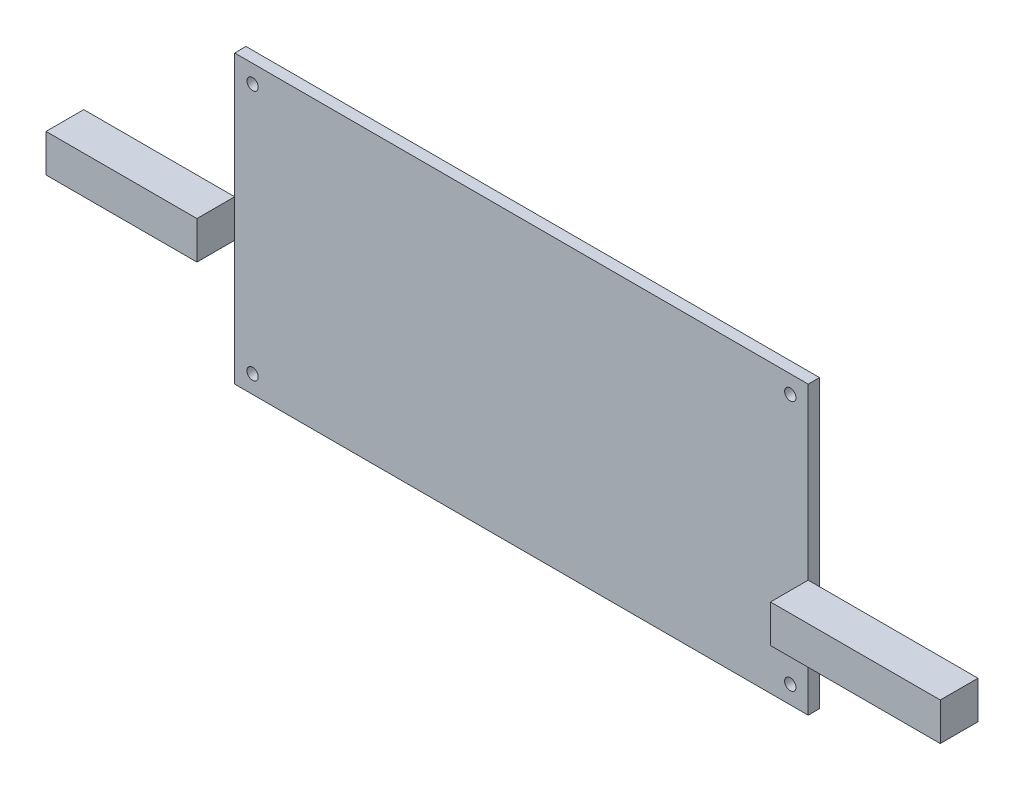
SolidWorks part; units mm, degrees
ref_plane "Front" through (0, 0, 0) normal (0, 0, 1) x (1, 0, 0)
ref_plane "Top" through (0, 0, 0) normal (0, 1, 0) x (1, 0, 0)
ref_plane "Right" through (0, 0, 0) normal (1, 0, 0) x (0, 0, -1)
sketch "Sketch1" plane through (0, 0, 0) normal (0, 0, 1) x (1, 0, 0)
  line L1 (-76, -38) -> (76, -38)
  line L2 (-76, -38) -> (-76, 38)
  line L3 (-76, 38) -> (76, 38)
  line L4 (76, -38) -> (76, 38)
  line L5 (-76, -38) -> (76, 38) construction
  line L6 (-76, 38) -> (76, -38) construction
  point P0 (0, 0)
  dimension "D1" = 152
  dimension "D2" = 76
extrude "Boss-Extrude1" add sketch "Sketch1" along normal mid plane 3
sketch "Sketch3" plane through (0, 0, 0) normal (0, 0, 1) x (1, 0, 0)
  line L1 (-71.25, -33.25) -> (71.25, -33.25) construction
  line L2 (-71.25, -33.25) -> (-71.25, 33.25) construction
  line L3 (-71.25, 33.25) -> (71.25, 33.25) construction
  line L4 (71.25, -33.25) -> (71.25, 33.25) construction
  line L5 (-71.25, -33.25) -> (71.25, 33.25) construction
  line L6 (-71.25, 33.25) -> (71.25, -33.25) construction
  circle A2 centre (-71.25, 33.25) radius 1.5
  circle A3 centre (71.25, 33.25) radius 1.5
  circle A4 centre (-71.25, -33.25) radius 1.5
  circle A5 centre (71.25, -33.25) radius 1.5
  point P0 (0, 0)
  point P10 (-71.25, -33.25)
  point P12 (71.25, -33.25)
  dimension "D3" = 3
  dimension "D1" = 142.5
  dimension "D2" = 66.5
extrude "Cut-Extrude1" cut sketch "Sketch3" against normal through all both and the other way through all
sketch "Sketch4" plane through (0, 0, 1.5) normal (0, 0, 1) x (1, 0, 0)
  line L0 (-76, 38) -> (-76, -38) construction
  line L1 (-76, 5) -> (-116, 5)
  line L2 (-76, 5) -> (-76, -5)
  line L3 (-76, -5) -> (-116, -5)
  line L4 (-116, 5) -> (-116, -5)
  line L5 (76, -38) -> (76, 38) construction
  line L6 (76, -7) -> (121, -7)
  line L7 (76, -7) -> (76, -17)
  line L8 (76, -17) -> (121, -17)
  line L9 (121, -7) -> (121, -17)
  line L10 (76, 38) -> (-76, 38) construction
  point P12 (-76, 0)
  point P14 (76, -12)
  dimension "D1" = 40
  dimension "D2" = 45
  dimension "D3" = 10
  dimension "D4" = 50
extrude "Boss-Extrude2" add sketch "Sketch4" along normal blind 10 separate body
